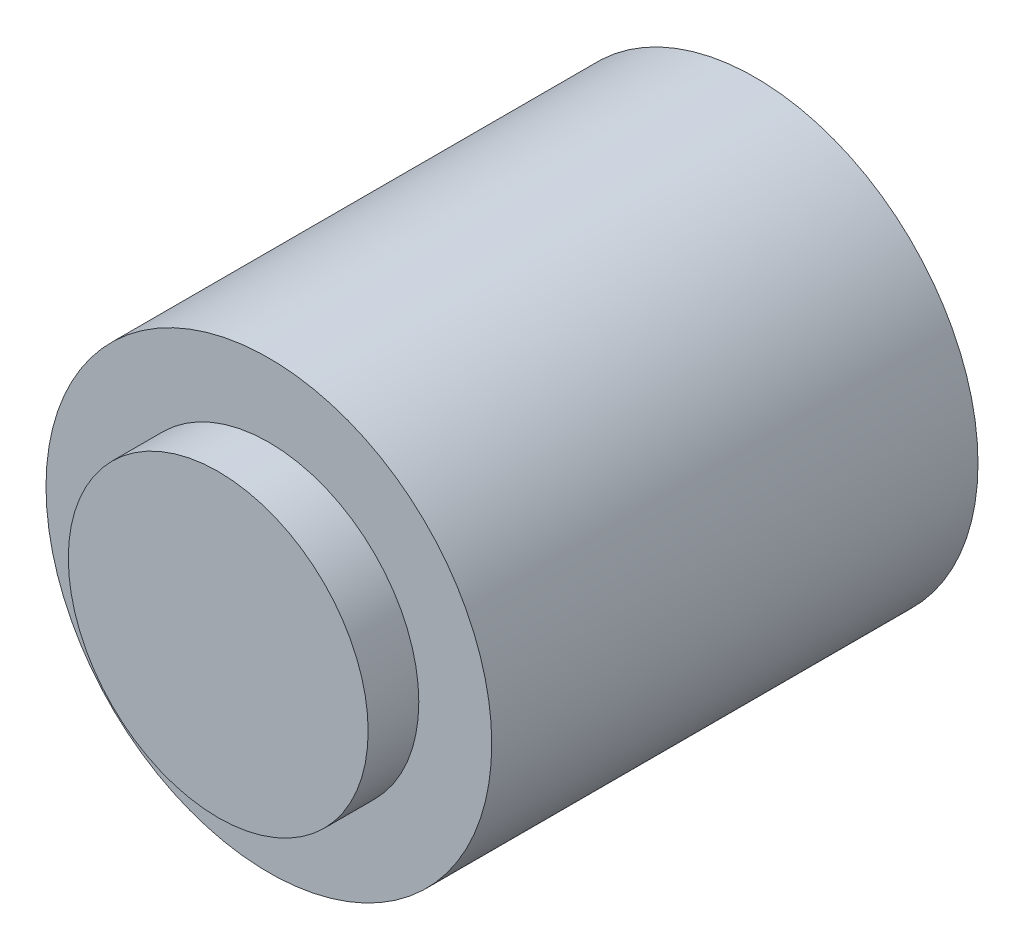
SolidWorks part; units mm, degrees
ref_plane "Front Plane" through (0, 0, 0) normal (0, 0, 1) x (1, 0, 0)
ref_plane "Top Plane" through (0, 0, 0) normal (0, 1, 0) x (1, 0, 0)
ref_plane "Right Plane" through (0, 0, 0) normal (1, 0, 0) x (0, 0, -1)
sketch "Sketch1" plane through (0, 0, 0) normal (0, 0, 1) x (1, 0, 0)
  circle A0 centre (0, 0) radius 11
  dimension "D1" = 22
extrude "Extrude1" add sketch "Sketch1" along normal blind 24
sketch "Sketch2" plane through (0, 0, 24) normal (0, 0, 1) x (1, 0, 0)
  circle A0 centre (0, 0) radius 7.4
  dimension "D1" = 14.8
extrude "Extrude3" add sketch "Sketch2" along normal blind 2.5
sketch "Sketch3" plane through (0, 0, 0) normal (0, 0, -1) x (-1, 0, 0)
  circle A0 centre (0, 0) radius 3.65
  dimension "D1" = 7.3
extrude "Extrude4" add sketch "Sketch3" along normal blind 1.3
sketch "Sketch4" plane through (0, 0, -1.3) normal (0, 0, -1) x (-1, 0, 0)
  circle A0 centre (0, 0) radius 1.5
  dimension "D1" = 3
extrude "Extrude5" add sketch "Sketch4" along normal blind 5
